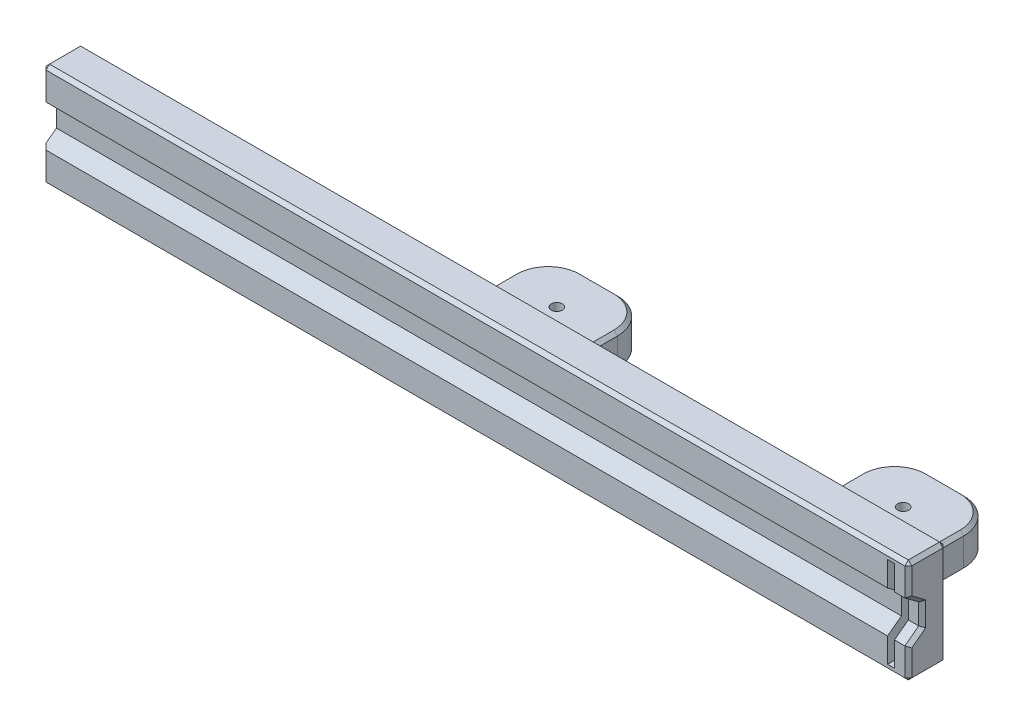
SolidWorks part; units mm, degrees
ref_plane "前基準面" through (0, 0, 0) normal (0, 0, 1) x (1, 0, 0)
ref_plane "上基準面" through (0, 0, 0) normal (0, 1, 0) x (1, 0, 0)
ref_plane "右基準面" through (0, 0, 0) normal (1, 0, 0) x (0, 0, -1)
sketch "草圖1" plane through (0, 0, 0) normal (0, 0, 1) x (1, 0, 0)
  line L0 (0, 0) -> (250, 0)
  line L1 (250, 0) -> (250, 30)
  line L2 (250, 30) -> (0, 30)
  line L3 (0, 30) -> (0, 0)
  dimension "D1" = 30
  dimension "D2" = 250
extrude "填料-伸長1" add sketch "草圖1" along normal blind 11
sketch "草圖4" plane through (0, 0, 0) normal (0, 0, -1) x (-1, 0, 0)
  line L0 (-250, 15) -> (0, 15)
  line L1 (-250, 0) -> (-250, 30) construction
  line L2 (0, 30) -> (0, 0) construction
  line L3 (-125, 30) -> (-125, 0)
  line L4 (-250, 30) -> (0, 30) construction
  line L5 (0, 0) -> (-250, 0) construction
  line L6 (-140, 15) -> (-125, 15)
  line L7 (-125, 15) -> (-110, 15)
  line L8 (-140, 15) -> (-140, 20)
  line L9 (-140, 20) -> (-110, 20)
  line L10 (-110, 20) -> (-110, 15)
  line L11 (-140, 15) -> (-140, 10)
  line L12 (-140, 10) -> (-125, 10)
  line L13 (-125, 10) -> (-110, 10)
  line L14 (-110, 10) -> (-110, 15)
  line L16 (-164.6389, 10) -> (-194.6389, 10)
  line L17 (-164.6389, 10) -> (-164.6389, 20)
  line L18 (-164.6389, 20) -> (-194.6389, 20)
  line L19 (-194.6389, 10) -> (-194.6389, 20)
  line L20 (-164.6389, 10) -> (-194.6389, 20) construction
  line L21 (-164.6389, 20) -> (-194.6389, 10) construction
  point P17 (-179.6389, 15)
  dimension "D1" = 15
  dimension "D2" = 15
  dimension "D3" = 5
  dimension "D4" = 5
  dimension "D5" = 10
  dimension "D6" = 30
extrude "填料-伸長2" add sketch "草圖4" along normal blind 25 contours L11 L12 L3 L0 | L9 L8 L0 L3 | L10 L9 L3 L0 | L13 L14 L0 L3
sketch "草圖5" plane through (250, 0, 0) normal (1, 0, 0) x (0, 0, -1)
  line L0 (-11, 30) -> (-11, 21)
  line L1 (-11, 0) -> (-11, 30) construction
  line L2 (-7, 15) -> (-7, 12)
  line L3 (-7, 15) -> (-7, 18)
  line L4 (-7, 18) -> (-11, 21)
  line L5 (-11, 9) -> (-11, 0)
  line L6 (-11, 15) -> (0, 15)
  line L7 (0, 30) -> (0, 0) construction
  line L8 (-7, 12) -> (-11, 9)
  line L9 (-11, 9) -> (-11, 21)
  line M6 (-11, 30) -> (-11, 0)
  dimension "D1" = 12
  dimension "D2" = 30
  dimension "D3" = 6
  dimension "D4" = 3
  dimension "D5" = 3
  dimension "D6" = 4
extrude "除料-伸長2" cut sketch "草圖5" against normal through all contours L6 L3 L4 M6 | L8 L2 L6 M6
sketch "草圖6" plane through (0, 10, 0) normal (0, -1, 0) x (1, 0, 0)
  line L0 (125, 0) -> (125, -25)
  line L1 (250, 0) -> (0, 0) construction
  line L2 (140, -25) -> (110, -25) construction
  line L3 (110, -12.5) -> (140, -12.5)
  line L4 (110, -25) -> (110, 0) construction
  line L5 (140, -25) -> (140, 0) construction
  circle A0 centre (125, -12.5) radius 1.6
  dimension "D1" = 3.2
extrude "除料-伸長3" cut sketch "草圖6" against normal through all contours L3 A0 L0 | L0 A0 L3 | L3 A0 L0 | L0 A0 L3
sketch "草圖7" plane through (0, 10, 0) normal (0, -1, 0) x (1, 0, 0)
  line L0 (125, -14.1) -> (125, -25)
  line L1 (140, -25) -> (110, -25) construction
  circle A0 centre (125, -12.5) radius 1.6 construction
sketch "草圖9" plane through (0, 0, 0) normal (0, 0, -1) x (-1, 0, 0)
  line L1 (-194.6389, 20) -> (-164.6389, 20)
  line L2 (-194.6389, 20) -> (-194.6389, 10)
  line L3 (-194.6389, 10) -> (-164.6389, 10)
  line L4 (-164.6389, 20) -> (-164.6389, 10)
  line L5 (-194.6389, 20) -> (-164.6389, 10) construction
  line L6 (-194.6389, 10) -> (-164.6389, 20) construction
  point P0 (-179.6389, 15)
sketch "草圖11" plane through (0, 0, 0) normal (0, 0, -1) x (-1, 0, 0)
  line L0 (-125, 15) -> (-225, 15)
  line L1 (-250, 15) -> (0, 15) construction
  line L3 (-240, 10) -> (-210, 10)
  line L4 (-240, 10) -> (-240, 20)
  line L5 (-240, 20) -> (-210, 20)
  line L6 (-210, 10) -> (-210, 20)
  line L7 (-240, 10) -> (-210, 20) construction
  line L8 (-240, 20) -> (-210, 10) construction
  dimension "D1" = 100
  dimension "D2" = 10
  dimension "D3" = 30
extrude "填料-伸長4" add sketch "草圖11" along normal blind 25
sketch "草圖12" plane through (0, 20, 0) normal (0, 1, 0) x (1, 0, 0)
  line L0 (240, 12.5) -> (210, 12.5)
  line L1 (240, 25) -> (240, 0) construction
  line L2 (210, 25) -> (210, 0) construction
  circle A0 centre (225, 12.5) radius 1.6
  dimension "D1" = 3.2
extrude "除料-伸長5" cut sketch "草圖12" against normal through all contours A0
fillet "圓角1" radius 10 4 edges at (110, 15, -25) (140, 15, -25) (210, 15, -25) (240, 15, -25)
sketch "草圖13" plane through (0, 0, 11) normal (0, 0, 1) x (1, 0, 0)
  line L1 (244, 28.1) -> (246, 28.1)
  line L2 (244, 28.1) -> (244, 1.9)
  line L3 (244, 1.9) -> (246, 1.9)
  line L4 (246, 28.1) -> (246, 1.9)
  line L5 (250, 15) -> (0, 15) construction
  line L6 (250, 0) -> (250, 30) construction
  dimension "D1" = 2
  dimension "D2" = 26.2
  dimension "D3" = 13.1
  dimension "D4" = 4
extrude "除料-伸長6" cut sketch "草圖13" against normal through all
chamfer "導角1" distance 1 angle 45 45 edges at (250, 15, 0) (250, 30, 5.5) (250, 0, 5.5) (125, 30, 11) (125, 0, 11) (0, 30, 5.5) (125, 30, 0) (125, 0, 0) (0, 15, 0) (0, 0, 5.5) (225, 10, -25) (225, 20, -25) (212.9289, 20, -22.0711) (212.9289, 10, -22.0711) (237.0711, 10, -22.0711) (237.0711, 20, -22.0711) (225, 20, 0) (210, 20, -7.5) (210, 15, 0) (210, 10, -7.5) (225, 10, 0) (240, 10, -7.5) (240, 15, 0) (240, 20, -7.5) (125, 20, -25) (125, 10, -25) (112.9289, 20, -22.0711) (112.9289, 10, -22.0711) (137.0711, 20, -22.0711) (137.0711, 10, -22.0711) (110, 20, -7.5) (125, 10, 0) (110, 10, -7.5) (110, 15, 0) (125, 20, 0) (140, 20, -7.5) (140, 15, 0) (140, 10, -7.5) (250, 4.5, 11) (250, 10.5, 9) (250, 15, 7) (250, 19.5, 9) (250, 25.5, 11) (0, 25.5, 11) (0, 4.5, 11)
